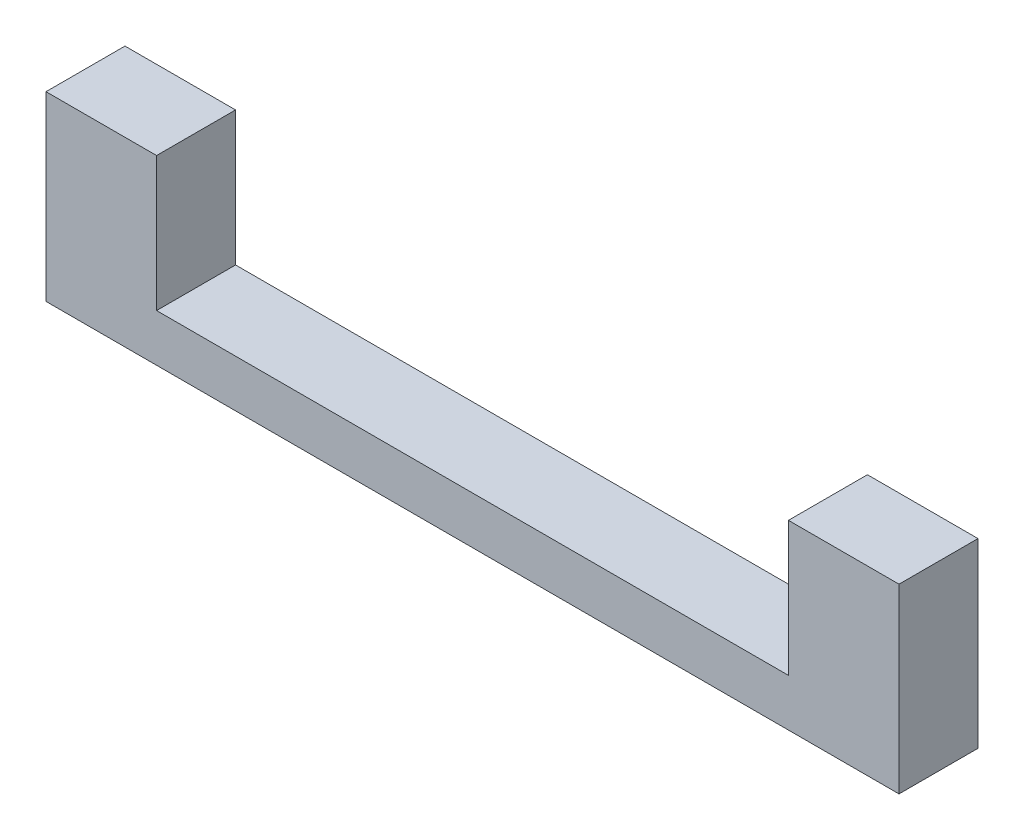
SolidWorks part; units mm, degrees
ref_plane "Front Plane" through (0, 0, 0) normal (0, 0, 1) x (1, 0, 0)
ref_plane "Top Plane" through (0, 0, 0) normal (0, 1, 0) x (1, 0, 0)
ref_plane "Right Plane" through (0, 0, 0) normal (1, 0, 0) x (0, 0, -1)
sketch "Sketch1" plane through (0, 0, 0) normal (1, 0, 0) x (0, 0, -1)
  line L0 (0, 0) -> (1.6017, 0) construction
  line L1 (1.705, 2.9531) -> (-1.705, 2.9531)
  line L2 (-1.705, 2.9531) -> (-3.41, 0)
  line L3 (-3.41, 0) -> (-1.705, -2.9531)
  line L4 (-1.705, -2.9531) -> (1.705, -2.9531)
  line L5 (1.705, -2.9531) -> (3.41, 0)
  line L6 (3.41, 0) -> (1.705, 2.9531)
  line L8 (-4.25, -4.25) -> (4.25, -4.25)
  line L9 (-4.25, -4.25) -> (-4.25, 4.25)
  line L10 (-4.25, 4.25) -> (4.25, 4.25)
  line L11 (4.25, -4.25) -> (4.25, 4.25)
  line L12 (-4.25, -4.25) -> (4.25, 4.25) construction
  line L13 (-4.25, 4.25) -> (4.25, -4.25) construction
  circle A0 centre (0, 0) radius 2.9531 construction
  dimension "D1" = 3.41
  dimension "D2" = 8.5
  dimension "D3" = 8.5
extrude "Boss-Extrude1" add sketch "Sketch1" along normal blind 5
sketch "Sketch2" plane through (0, 0, 0) normal (-1, 0, 0) x (0, 0, 1)
  line L1 (-4.25, -4.25) -> (4.25, -4.25)
  line L2 (-4.25, -4.25) -> (-4.25, 4.25)
  line L3 (-4.25, 4.25) -> (4.25, 4.25)
  line L4 (4.25, -4.25) -> (4.25, 4.25)
  line L5 (-4.25, -4.25) -> (4.25, 4.25) construction
  line L6 (-4.25, 4.25) -> (4.25, -4.25) construction
  point P0 (0, 0)
extrude "Boss-Extrude2" add sketch "Sketch2" along normal blind 2
sketch "Sketch3" plane through (0, 0, 0) normal (1, 0, 0) x (0, 0, -1)
  circle A0 centre (0, 0) radius 1.5
  dimension "D1" = 3
extrude "Cut-Extrude1" cut sketch "Sketch3" against normal blind 2
sketch "Sketch4" plane through (0, -4.25, 0) normal (0, -1, 0) x (1, 0, 0)
  line L0 (5, -4.25) -> (-2, -4.25) construction
  line L1 (-2, 4.25) -> (52, 4.25)
  line L2 (-2, 4.25) -> (-2, -4.25)
  line L3 (-2, -4.25) -> (52, -4.25)
  line L4 (52, 4.25) -> (52, -4.25)
  dimension "D1" = 54
extrude "Boss-Extrude3" add sketch "Sketch4" along normal blind 3
sketch "Sketch5" plane through (0, -4.25, 0) normal (0, 1, 0) x (1, 0, 0)
  line L0 (52, -4.25) -> (5, -4.25) construction
  line L1 (52, 4.25) -> (45, 4.25)
  line L2 (52, 4.25) -> (52, -4.25)
  line L3 (52, -4.25) -> (45, -4.25)
  line L4 (45, 4.25) -> (45, -4.25)
  dimension "D1" = 7
extrude "Boss-Extrude4" add sketch "Sketch5" along normal up to surface (8.5 mm away) up to face at (1.5, 4.25, 0)
sketch "Sketch6" plane through (45, 0, 0) normal (-1, 0, 0) x (0, 0, 1)
  line L0 (-4.25, -4.25) -> (4.25, -4.25) construction
  line L1 (3.41, 0) -> (1.705, 2.9531)
  line L2 (1.705, 2.9531) -> (-1.705, 2.9531)
  line L3 (-1.705, 2.9531) -> (-3.41, 0)
  line L4 (-3.41, 0) -> (-1.705, -2.9531)
  line L5 (-1.705, -2.9531) -> (1.705, -2.9531)
  line L6 (1.705, -2.9531) -> (3.41, 0)
  circle A0 centre (0, 0) radius 2.9531 construction
  dimension "D1" = 3.41
sketch "Sketch7" plane through (50, 0, 0) normal (-1, 0, 0) x (0, 0, 1)
  circle A0 centre (0, 0) radius 1.5
  dimension "D1" = 3
sketch "Sketch8" plane through (0, 0, 0) normal (1, 0, 0) x (0, 0, -1)
  line L0 (-1.705, 2.9531) -> (-3.41, 0) construction
  line L1 (-3.41, 0) -> (-1.705, -2.9531) construction
  line L2 (-1.705, -2.9531) -> (1.705, -2.9531) construction
  line L3 (1.705, -2.9531) -> (3.41, 0) construction
  line L4 (3.41, 0) -> (1.705, 2.9531) construction
  line L5 (1.705, 2.9531) -> (-1.705, 2.9531) construction
  line L6 (-1.705, 2.9531) -> (-3.41, 0)
  line L7 (-3.41, 0) -> (-1.705, -2.9531)
  line L8 (-1.705, -2.9531) -> (1.705, -2.9531)
  line L9 (1.705, -2.9531) -> (3.41, 0)
  line L10 (3.41, 0) -> (1.705, 2.9531)
  line L11 (1.705, 2.9531) -> (-1.705, 2.9531)
  circle A0 centre (0, 0) radius 1.5 construction
  circle A1 centre (0, 0) radius 1.5
extrude "Boss-Extrude5" add sketch "Sketch8" along normal blind 2.5
sketch "Sketch9" plane through (50, 0, 0) normal (-1, 0, 0) x (0, 0, 1)
  line L0 (3.41, 0) -> (1.705, 2.9531) construction
  line L1 (1.705, -2.9531) -> (3.41, 0) construction
  line L2 (-1.705, -2.9531) -> (1.705, -2.9531) construction
  line L3 (-3.41, 0) -> (-1.705, -2.9531) construction
  line L4 (1.705, 2.9531) -> (-1.705, 2.9531) construction
  line L5 (-1.705, 2.9531) -> (-3.41, 0) construction
  line L6 (3.41, 0) -> (1.705, 2.9531)
  line L7 (1.705, -2.9531) -> (3.41, 0)
  line L8 (-1.705, -2.9531) -> (1.705, -2.9531)
  line L9 (-3.41, 0) -> (-1.705, -2.9531)
  line L10 (1.705, 2.9531) -> (-1.705, 2.9531)
  line L11 (-1.705, 2.9531) -> (-3.41, 0)
  circle A0 centre (0, 0) radius 1.5 construction
  circle A1 centre (0, 0) radius 1.5
extrude "Boss-Extrude6" add sketch "Sketch9" along normal blind 2.5
sketch "Sketch10" plane through (5, 0, 0) normal (1, 0, 0) x (0, 0, -1)
  line L0 (3.41, 0) -> (1.705, 2.9531) construction
  line L1 (1.705, -2.9531) -> (3.41, 0) construction
  line L2 (-1.705, -2.9531) -> (1.705, -2.9531) construction
  line L3 (-3.41, 0) -> (-1.705, -2.9531) construction
  line L4 (-1.705, 2.9531) -> (-3.41, 0) construction
  line L5 (1.705, 2.9531) -> (-1.705, 2.9531) construction
  line L6 (3.41, 0) -> (1.705, 2.9531)
  line L7 (1.705, -2.9531) -> (3.41, 0)
  line L8 (-1.705, -2.9531) -> (1.705, -2.9531)
  line L9 (-3.41, 0) -> (-1.705, -2.9531)
  line L10 (-1.705, 2.9531) -> (-3.41, 0)
  line L11 (1.705, 2.9531) -> (-1.705, 2.9531)
  line L13 (-4.25, 4.25) -> (4.25, 4.25)
  line L14 (-4.25, 4.25) -> (-4.25, -4.25)
  line L15 (-4.25, -4.25) -> (4.25, -4.25)
  line L16 (4.25, 4.25) -> (4.25, -4.25)
extrude "Boss-Extrude7" add sketch "Sketch10" along normal blind 1
sketch "Sketch11" plane through (45, 0, 0) normal (-1, 0, 0) x (0, 0, 1)
  line L0 (-3.41, 0) -> (-1.705, -2.9531) construction
  line L1 (-1.705, -2.9531) -> (1.705, -2.9531) construction
  line L2 (1.705, -2.9531) -> (3.41, 0) construction
  line L3 (3.41, 0) -> (1.705, 2.9531) construction
  line L4 (1.705, 2.9531) -> (-1.705, 2.9531) construction
  line L5 (-1.705, 2.9531) -> (-3.41, 0) construction
  line L6 (-3.41, 0) -> (-1.705, -2.9531)
  line L7 (-1.705, -2.9531) -> (1.705, -2.9531)
  line L8 (1.705, -2.9531) -> (3.41, 0)
  line L9 (3.41, 0) -> (1.705, 2.9531)
  line L10 (1.705, 2.9531) -> (-1.705, 2.9531)
  line L11 (-1.705, 2.9531) -> (-3.41, 0)
  line L13 (-4.25, 4.25) -> (4.25, 4.25)
  line L14 (-4.25, 4.25) -> (-4.25, -4.25)
  line L15 (-4.25, -4.25) -> (4.25, -4.25)
  line L16 (4.25, 4.25) -> (4.25, -4.25)
sketch "Sketch12" plane through (2.5, 0, 0) normal (1, 0, 0) x (0, 0, -1)
  line L0 (1.705, -2.9531) -> (3.41, 0) construction
  line L1 (3.41, 0) -> (1.705, 2.9531) construction
  line L2 (-1.705, -2.9531) -> (1.705, -2.9531) construction
  line L3 (1.705, 2.9531) -> (-1.705, 2.9531) construction
  line L4 (-3.41, 0) -> (-1.705, -2.9531) construction
  line L5 (-1.705, 2.9531) -> (-3.41, 0) construction
  line L6 (1.705, -2.9531) -> (3.41, 0)
  line L7 (3.41, 0) -> (1.705, 2.9531)
  line L8 (-1.705, -2.9531) -> (1.705, -2.9531)
  line L9 (1.705, 2.9531) -> (-1.705, 2.9531)
  line L10 (-3.41, 0) -> (-1.705, -2.9531)
  line L11 (-1.705, 2.9531) -> (-3.41, 0)
extrude "Cut-Extrude4" cut sketch "Sketch12" against normal blind 0.5
sketch "Sketch13" plane through (47.5, 0, 0) normal (-1, 0, 0) x (0, 0, 1)
  line L0 (1.705, 2.9531) -> (-1.705, 2.9531) construction
  line L1 (-1.705, 2.9531) -> (-3.41, 0) construction
  line L2 (-3.41, 0) -> (-1.705, -2.9531) construction
  line L3 (-1.705, -2.9531) -> (1.705, -2.9531) construction
  line L4 (1.705, -2.9531) -> (3.41, 0) construction
  line L5 (3.41, 0) -> (1.705, 2.9531) construction
  line L6 (1.705, 2.9531) -> (-1.705, 2.9531)
  line L7 (-1.705, 2.9531) -> (-3.41, 0)
  line L8 (-3.41, 0) -> (-1.705, -2.9531)
  line L9 (-1.705, -2.9531) -> (1.705, -2.9531)
  line L10 (1.705, -2.9531) -> (3.41, 0)
  line L11 (3.41, 0) -> (1.705, 2.9531)
extrude "Cut-Extrude5" cut sketch "Sketch13" against normal blind 0.5
sketch "Sketch14" plane through (6, 0, 0) normal (1, 0, 0) x (0, 0, -1)
  line L1 (-4.25, 4.25) -> (4.25, 4.25)
  line L2 (-4.25, 4.25) -> (-4.25, -4.25)
  line L3 (-4.25, -4.25) -> (4.25, -4.25)
  line L4 (4.25, 4.25) -> (4.25, -4.25)
extrude "Boss-Extrude8" add sketch "Sketch14" against normal up to surface (8 mm away) up to face at (-2, 0, -1.5)
sketch "Sketch15" plane through (6, 0, 0) normal (1, 0, 0) x (0, 0, -1)
  line L1 (-4.25, 4.25) -> (4.25, 4.25)
  line L2 (-4.25, 4.25) -> (-4.25, -4.25)
  line L3 (-4.25, -4.25) -> (4.25, -4.25)
  line L4 (4.25, 4.25) -> (4.25, -4.25)
extrude "Cut-Extrude6" cut sketch "Sketch15" against normal blind 1
sketch "Sketch16" plane through (0, 4.25, 0) normal (0, 1, 0) x (1, 0, 0)
  line L0 (52, 4.25) -> (52, -4.25) construction
  line L1 (-2, 4.25) -> (52, 4.25)
  line L2 (-2, 4.25) -> (-2, 0.75)
  line L3 (-2, 0.75) -> (52, 0.75)
  line L4 (52, 4.25) -> (52, 0.75)
  dimension "D1" = 3.5
extrude "Cut-Extrude7" cut sketch "Sketch16" against normal blind 15
sketch "Sketch17" plane through (45, 0, 0) normal (-1, 0, 0) x (0, 0, 1)
  line L1 (-0.75, 4.25) -> (4.25, 4.25)
  line L2 (-0.75, 4.25) -> (-0.75, -4.25)
  line L3 (-0.75, -4.25) -> (4.25, -4.25)
  line L4 (4.25, 4.25) -> (4.25, -4.25)
extrude "Boss-Extrude9" add sketch "Sketch17" against normal up to surface (7 mm away) up to face at (52, -1.5, 1.75)
